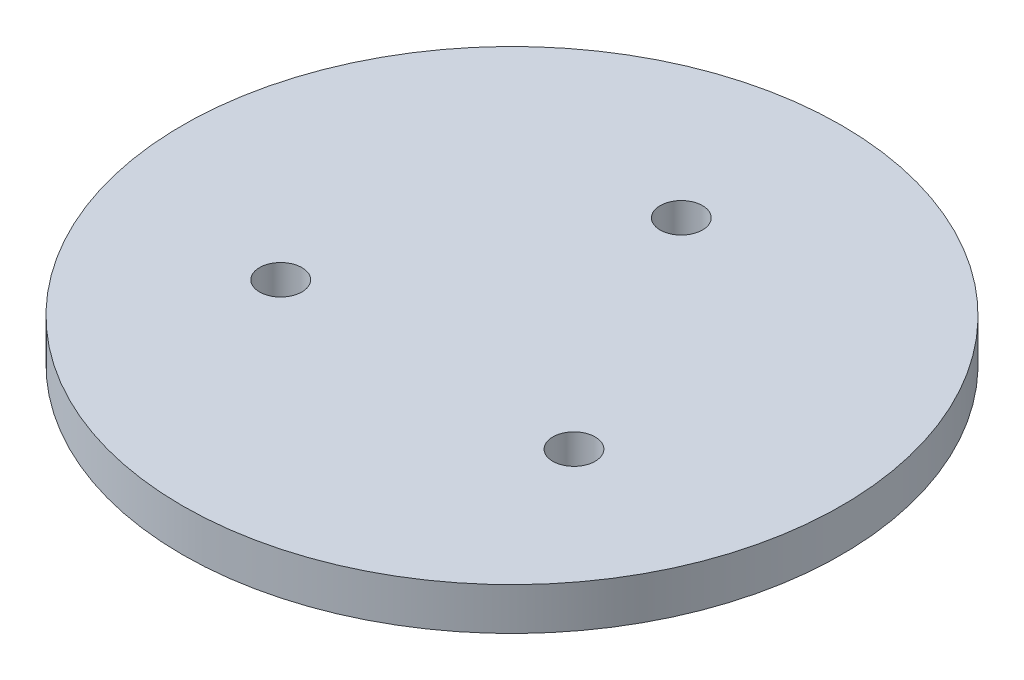
SolidWorks part; units mm, degrees
ref_plane "前视基准面" through (0, 0, 0) normal (0, 0, 1) x (1, 0, 0)
ref_plane "上视基准面" through (0, 0, 0) normal (0, 1, 0) x (1, 0, 0)
ref_plane "右视基准面" through (0, 0, 0) normal (1, 0, 0) x (0, 0, -1)
sketch "草图1" plane through (0, 0, 0) normal (0, 1, 0) x (1, 0, 0)
  circle A0 centre (0, 0) radius 77.8539
  circle A1 centre (0, 40) radius 5
  circle A2 centre (34.641, -20) radius 5
  circle A3 centre (-34.641, -20) radius 5
  point P11 (0, 0)
  dimension "D1" = 10
  dimension "D2" = 40
  dimension "D3" = 3
extrude "凸台-拉伸1" add sketch "草图1" along normal blind 10
sketch "草图2" plane through (0, 10, 0) normal (0, 1, 0) x (1, 0, 0)
  text T0 "A"
  text T1 "B"
  text T2 "C"
  point P3 (30.7802, -30.7558)
  point P4 (0, 0)
